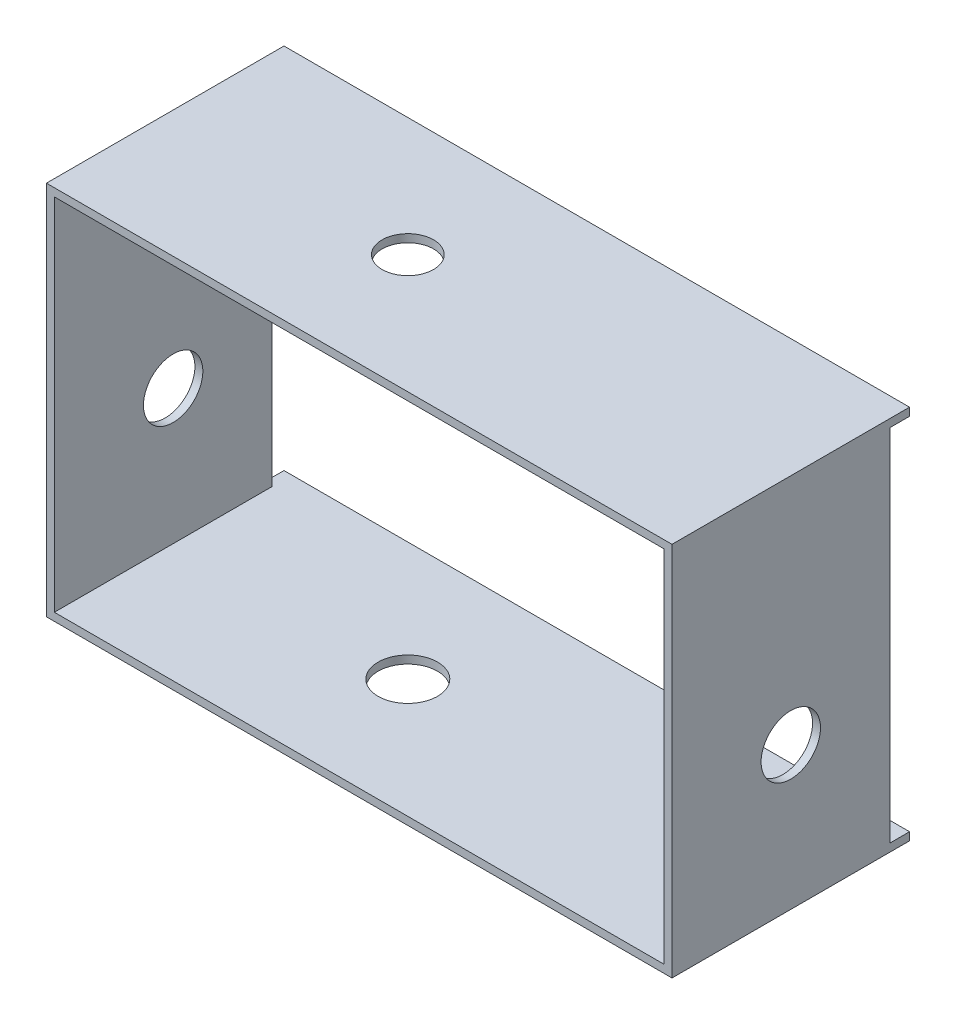
SolidWorks part; units mm, degrees
ref_plane "Front Plane" through (0, 0, 0) normal (0, 0, 1) x (1, 0, 0)
ref_plane "Top Plane" through (0, 0, 0) normal (0, 1, 0) x (1, 0, 0)
ref_plane "Right Plane" through (0, 0, 0) normal (1, 0, 0) x (0, 0, -1)
sketch "Sketch4" plane through (0, 0, 0) normal (0, 1, 0) x (1, 0, 0)
  line L0 (0, 0) -> (195.58, 0)
  line L1 (195.58, 0) -> (195.58, 76.2)
  line L2 (0, 0) -> (0, 76.2)
  line L3 (0, 76.2) -> (195.58, 76.2)
  circle A0 centre (75.2856, 38.1) radius 8.255
extrude "Boss-Extrude2" add sketch "Sketch4" along normal blind 2.54
sketch "Sketch5" plane through (195.58, 0, 0) normal (1, 0, 0) x (0, 0, -1)
  line L0 (76.2, 2.54) -> (76.2, 0)
  line L1 (76.2, 0) -> (69.85, 0)
  line L2 (0, 0) -> (76.2, 0) construction
  line L8 (0, 2.54) -> (76.2, 2.54)
  line L9 (0, 2.54) -> (76.2, 2.54)
  line L13 (0, 2.54) -> (0, 0)
sketch "Sketch7" plane through (195.58, 0, 0) normal (1, 0, 0) x (0, 0, -1)
  line L0 (0, 0) -> (0, -115.3962)
  line L1 (0, -115.3962) -> (0, -117.9362)
  line L2 (0, -117.9362) -> (76.2, -117.9362)
  line L3 (76.2, -117.9362) -> (76.2, -115.3962)
  line L4 (69.85, 0) -> (69.85, -115.3962)
  line L5 (69.85, -115.3962) -> (76.2, -115.3962)
  circle A0 centre (38.1, -72.2162) radius 9.525
  line M1 (0, 0) -> (76.2, 0)
  line M2 (76.2, 0) -> (76.2, 2.54)
  line M3 (76.2, 2.54) -> (0, 2.54)
  line M4 (0, 2.54) -> (0, 0)
extrude "Boss-Extrude4" add sketch "Sketch7" along normal blind 2.54 contours L5 L4 L0 L1 L2 L3 A0 M1 | M4 M1 M2 M3
sketch "Sketch9" plane through (0, -117.9362, 0) normal (0, -1, 0) x (-1, 0, 0)
  line L0 (-198.12, 0) -> (-195.58, 0)
  line L1 (-195.58, 0) -> (0, 0)
  line L2 (0, 0) -> (0, 76.2)
  line L3 (0, 76.2) -> (-195.58, 76.2)
  line L4 (-195.58, 76.2) -> (-198.12, 76.2)
  line L5 (-198.12, 76.2) -> (-198.12, 0)
  circle A0 centre (-75.2856, 38.1) radius 9.525
extrude "Boss-Extrude5" add sketch "Sketch9" against normal blind 2.54
sketch "Sketch10" plane through (0, 0, 0) normal (-1, 0, 0) x (0, 0, 1)
  line L0 (0, 2.54) -> (0, 0)
  line L1 (0, 0) -> (0, -115.3962)
  line L2 (0, -115.3962) -> (0, -117.9362)
  line L3 (0, -117.9362) -> (-76.2, -117.9362)
  line L4 (-76.2, -117.9362) -> (-76.2, -115.3962)
  line L5 (-76.2, -115.3962) -> (-69.85, -115.3962)
  line L6 (0, -115.3962) -> (-76.2, -115.3962) construction
  line L7 (-69.85, -115.3962) -> (-69.85, 0)
  line L8 (-76.2, 0) -> (0, 0) construction
  line L9 (-69.85, 0) -> (-76.2, 0)
  line L10 (-76.2, 0) -> (-76.2, 2.54)
  line L11 (-76.2, 2.54) -> (0, 2.54)
  circle A0 centre (-38.1, -72.2162) radius 9.525
extrude "Boss-Extrude6" add sketch "Sketch10" along normal blind 2.54
